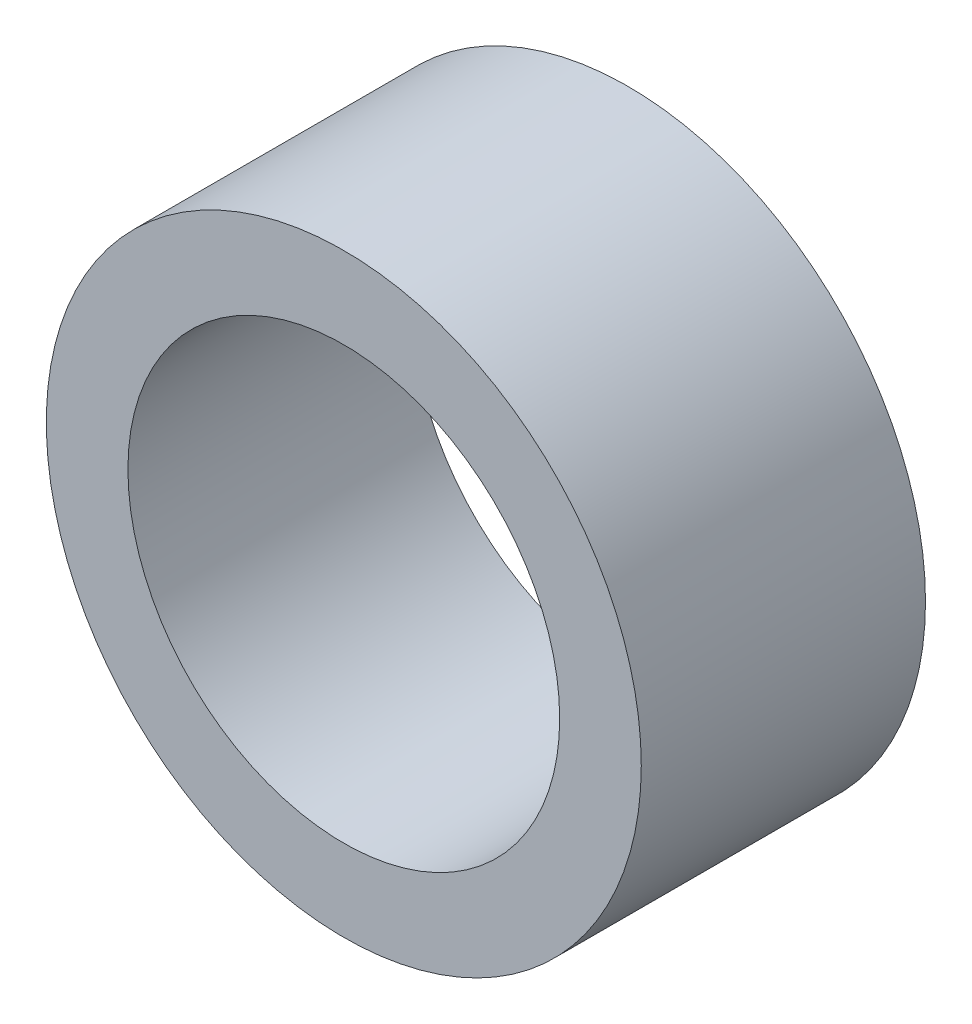
SolidWorks part; units mm, degrees
material "Delrin (Acetal)"
ref_plane "Front Plane" through (0, 0, 0) normal (0, 0, 1) x (1, 0, 0)
ref_plane "Top Plane" through (0, 0, 0) normal (0, 1, 0) x (1, 0, 0)
ref_plane "Right Plane" through (0, 0, 0) normal (1, 0, 0) x (0, 0, -1)
sketch "Sketch1" plane through (0, 0, 0) normal (0, 0, 1) x (1, 0, 0)
  circle A0 centre (0, 0) radius 11.1125
  circle A1 centre (0, 0) radius 8.0645
  dimension "D1" = 16.129
  dimension "Diameter" = 22.225
extrude "Extrude1" add sketch "Sketch1" along normal mid plane 10.6172
